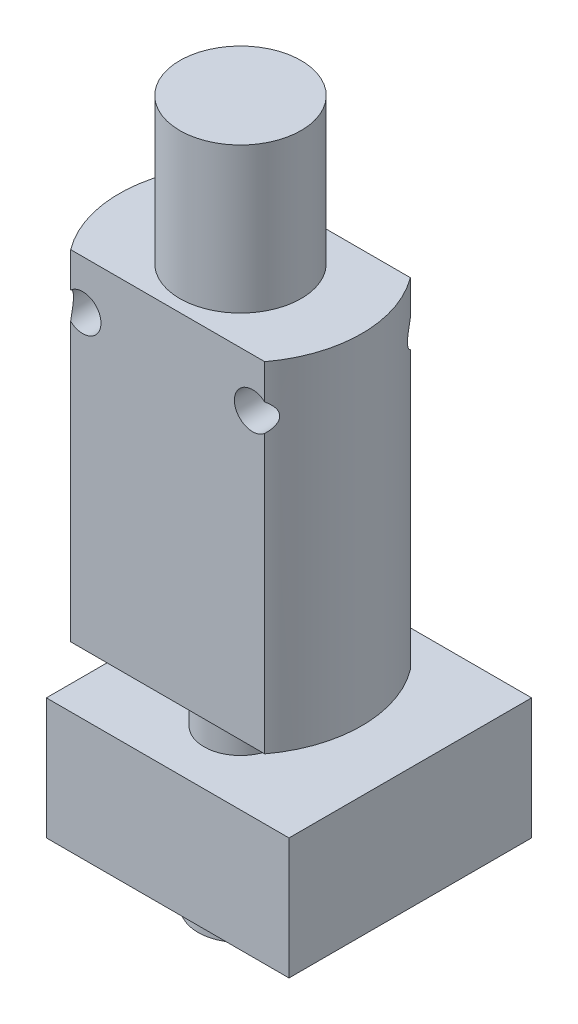
SolidWorks part; units mm, degrees
ref_plane "Plano frontal" through (0, 0, 0) normal (0, 0, 1) x (1, 0, 0)
ref_plane "Plano superior" through (0, 0, 0) normal (0, 1, 0) x (1, 0, 0)
ref_plane "Plano direito" through (0, 0, 0) normal (1, 0, 0) x (0, 0, -1)
sketch "Esboço1" plane through (0, 0, 0) normal (0, 0, 1) x (1, 0, 0)
  line L0 (0, 0) -> (0, 24.6707) construction
  line L2 (-10, 14) -> (10, 14)
  line L3 (-10, 14) -> (-10, -14)
  line L4 (-10, -14) -> (10, -14)
  line L5 (10, 14) -> (10, -14)
  line L6 (-10, 14) -> (10, -14) construction
  line L7 (-10, -14) -> (10, 14) construction
  circle A0 centre (-7, 10) radius 1.5
  circle A1 centre (7, 10) radius 1.5
  point P3 (0, 0)
  dimension "D4" = 3
  dimension "D1" = 28
  dimension "D2" = 20
  dimension "D3" = 14
  dimension "D5" = 4
extrude "Ressalto-extrusão1" add sketch "Esboço1" along normal mid plane 12
sketch "Esboço2" plane through (0, 0, 0) normal (0, 0, 1) x (1, 0, 0)
  line L0 (0, 0) -> (0, -34) construction
  line L1 (3, -29) -> (3, -19)
  line L3 (3, -29) -> (3.5, -29)
  line L4 (3.5, -29) -> (3.5, -32)
  line L5 (3.5, -32) -> (0.75, -34)
  line L6 (0.75, -34) -> (0, -34)
  line L7 (10, 14) -> (-10, 14) construction
  line L8 (3, -19) -> (3, -14)
  line L9 (-10, -14) -> (10, -14) construction
  line L10 (0, -34) -> (0, -14)
  line L11 (3, -14) -> (0, -14)
  line L12 (0, 26) -> (5, 26)
  line L13 (5, 26) -> (5, 14)
  line L14 (5, 14) -> (0, 14)
  line L15 (0, 26) -> (0, 14)
  dimension "D1" = 2
  dimension "D2" = 5
  dimension "D3" = 10
  dimension "D4" = 6
  dimension "D5" = 3
  dimension "D6" = 7
  dimension "D7" = 1.5
  dimension "D8" = 12
  dimension "D9" = 10
revolve "Revolução1" add sketch "Esboço2" angle 360 about L0
sketch "Esboço3" plane through (0, 0, 0) normal (0, 1, 0) x (1, 0, 0)
  line L0 (10, -6) -> (-10, -6) construction
  line L1 (-10, 14) -> (10, 14)
  line L2 (-10, 14) -> (-10, -6)
  line L3 (-10, -6) -> (10, -6)
  line L4 (10, 14) -> (10, -6)
  line L5 (-10, 14) -> (10, -6) construction
  line L6 (-10, -6) -> (10, 14) construction
  point P0 (0, 4)
  dimension "D1" = 20
extrude "Ressalto-extrusão2" add sketch "Esboço3" along normal blind 10 from surface at -29 starting at face at (0, -29, 3)
sketch "Esboço4" plane through (0, 14, 0) normal (0, 1, 0) x (1, 0, 0)
  line L0 (-8, 6) -> (-10, 6)
  line L1 (8, -6) -> (10, -6)
  line L4 (10, 6) -> (-10, 6)
  line L5 (-10, 6) -> (-10, -6)
  line L6 (-10, -6) -> (10, -6)
  line L7 (10, -6) -> (10, 6)
  line L8 (10, 6) -> (8, 6)
  line L9 (-10, 6) -> (-10, -6)
  line L10 (-10, -6) -> (-8, -6)
  line L11 (10, -6) -> (10, 6)
  arc A0 (-8, 6) -> (-8, -6) centre (0, 0) ccw
  arc A1 (8, -6) -> (8, 6) centre (0, 0) ccw
  line M6 (10, 6) -> (-10, 6)
  line M7 (-10, 6) -> (-10, -6)
  line M8 (-10, -6) -> (10, -6)
  line M9 (10, -6) -> (10, 6)
  dimension "D1" = 0
extrude "Corte-extrusão1" cut sketch "Esboço4" against normal up to surface (28 mm away) contours A0 M6 M7 | A0 L9 M8 | A1 M8 M9 | A1 L11 M6 up to face at (0, -14, 3)
